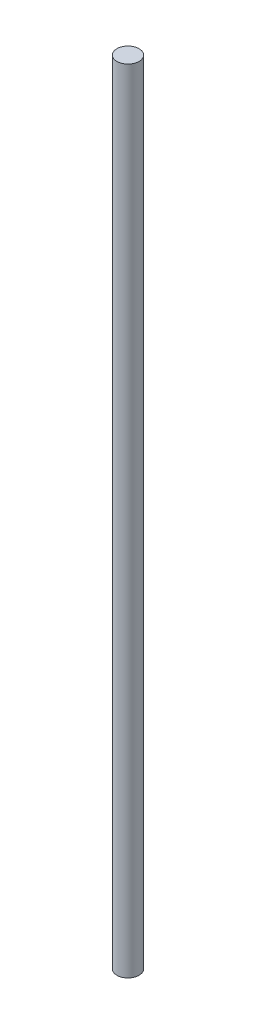
SolidWorks part; units mm, degrees
ref_plane "Front Plane" through (0, 0, 0) normal (0, 0, 1) x (1, 0, 0)
ref_plane "Top Plane" through (0, 0, 0) normal (0, 1, 0) x (1, 0, 0)
ref_plane "Right Plane" through (0, 0, 0) normal (1, 0, 0) x (0, 0, -1)
sketch "Sketch1" plane through (0, 0, 0) normal (0, 1, 0) x (1, 0, 0)
  circle A0 centre (0, 0) radius 4
extrude "Boss-Extrude1" add sketch "Sketch1" along normal blind 286
